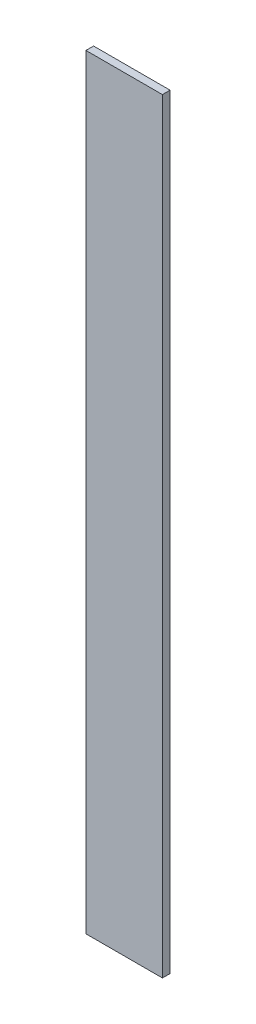
SolidWorks part; units mm, degrees
ref_plane "Front Plane" through (0, 0, 0) normal (0, 0, 1) x (1, 0, 0)
ref_plane "Top Plane" through (0, 0, 0) normal (0, 1, 0) x (1, 0, 0)
ref_plane "Right Plane" through (0, 0, 0) normal (1, 0, 0) x (0, 0, -1)
sketch "Sketch1" plane through (0, 0, 0) normal (0, 0, 1) x (1, 0, 0)
  line L1 (-10, -100) -> (10, -100)
  line L2 (-10, -100) -> (-10, 100)
  line L3 (-10, 100) -> (10, 100)
  line L4 (10, -100) -> (10, 100)
  line L5 (-10, -100) -> (10, 100) construction
  line L6 (-10, 100) -> (10, -100) construction
  point P0 (0, 0)
  dimension "D1" = 200
  dimension "D2" = 20
extrude "Boss-Extrude1" add sketch "Sketch1" along normal blind 2
